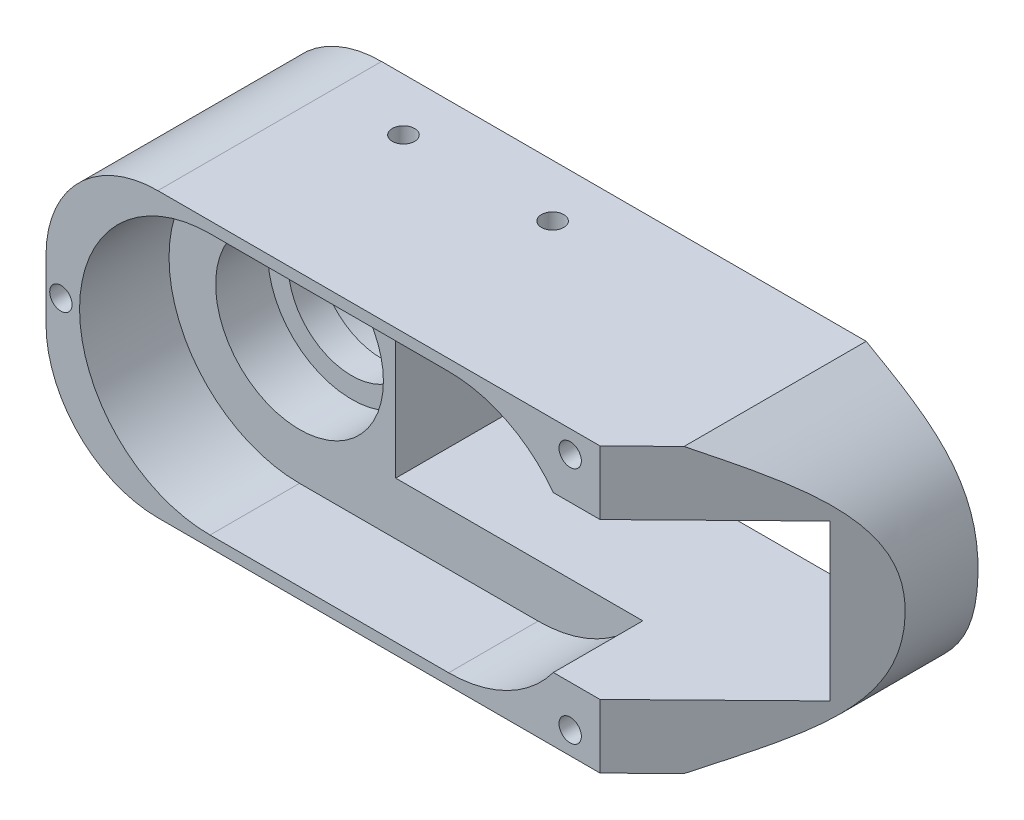
SolidWorks part; units mm, degrees
ref_plane "Front Plane" through (0, 0, 0) normal (0, 0, 1) x (1, 0, 0)
ref_plane "Top Plane" through (0, 0, 0) normal (0, 1, 0) x (1, 0, 0)
ref_plane "Right Plane" through (0, 0, 0) normal (1, 0, 0) x (0, 0, -1)
sketch "Sketch1" plane through (0, 0, 0) normal (0, 0, 1) x (1, 0, 0)
  line L1 (-50, 19) -> (30, 19)
  line L2 (-50, 19) -> (-50, -19)
  line L3 (-50, -19) -> (30, -19)
  spline S0 degree 3 poles (30, 19) (36.5612, 15.2119) (45.1601, 10.8287) (44.9676, -11.0883) (37.933, -14.4199) (30, -19) knots 0 0 0 0 0.445629 0.545629 1 1 1 1
  point P5 (-50, 0)
  dimension "D1" = 80
  dimension "D2" = 38
  dimension "D3" = 50
extrude "Extrude1" add sketch "Sketch1" along normal blind 30
sketch "Sketch2" plane through (0, 0, 30) normal (0, 0, 1) x (1, 0, 0)
  line L0 (-28, 17.5) -> (4, 17.5)
  line L1 (4, -17.5) -> (-28, -17.5)
  line L2 (-50, 19) -> (-50, -19) construction
  arc A0 (-28, 17.5) -> (-28, -17.5) centre (-28, 0) ccw
  arc A1 (4, -17.5) -> (4, 17.5) centre (4, 0) ccw
  dimension "D1" = 35
  dimension "D4" = 17.5
  dimension "D2" = 22
  dimension "D3" = 32
extrude "Extrude2" cut sketch "Sketch2" against normal blind 12
sketch "Sketch4" plane through (0, 0, 18) normal (0, 0, 1) x (1, 0, 0)
  line L0 (-28, 17.5) -> (-28, -17.5) construction
  circle A0 centre (-28, 0) radius 11.25
  arc A1 (-28, 17.5) -> (-28, -17.5) centre (-28, 0) ccw construction
  point P8 (0, 0)
  point P9 (-28, 0)
  dimension "D1" = 22.5
extrude "Extrude3" cut sketch "Sketch4" against normal blind 7
sketch "Sketch5" plane through (0, 0, 11) normal (0, 0, 1) x (1, 0, 0)
  circle A0 centre (-28, 0) radius 8.5
  circle A1 centre (-28, 0) radius 11.25 construction
  dimension "D1" = 17
extrude "Extrude4" cut sketch "Sketch5" against normal through all
sketch "Sketch6" plane through (0, 0, 0) normal (0, 0, -1) x (-1, 0, 0)
  circle A0 centre (28, 0) radius 11.25
  dimension "D1" = 22.5
extrude "Extrude5" cut sketch "Sketch6" against normal blind 7
sketch "Sketch8" plane through (0, 0, 18) normal (0, 0, 1) x (1, 0, 0)
  circle A0 centre (2, 0) radius 2.5
  circle A1 centre (-28, 0) radius 11.25 construction
  dimension "D1" = 5
  dimension "D2" = 30
extrude "Extrude6" cut sketch "Sketch8" against normal through all
sketch "Sketch7" plane through (0, 0, 0) normal (0, 0, -1) x (-1, 0, 0)
  line L0 (14.8, 0) -> (-2, 0) construction
  line L1 (-40.2, -10.4457) -> (14.8, -10.4457) construction
  line L2 (-40.2, -10.4457) -> (-40.2, 10.4457) construction
  line L3 (-40.2, 10.4457) -> (14.8, 10.4457) construction
  line L4 (14.8, -10.4457) -> (14.8, 10.4457) construction
  line L6 (7.8, 10.4457) -> (-33.2, 10.4457)
  line L7 (7.8, 10.4457) -> (7.8, -10.4457)
  line L8 (7.8, -10.4457) -> (-33.2, -10.4457)
  line L9 (-33.2, 10.4457) -> (-33.2, -10.4457)
  circle A1 centre (-2, 0) radius 2.5 construction
  point P14 (-12.7, -10.4457)
  point P15 (-12.7, -10.4457)
  dimension "D3" = 41
  dimension "D1" = 55
  dimension "D2" = 9.8
extrude "Extrude7" cut sketch "Sketch7" against normal through all
sketch "Sketch10" plane through (0, 0, 30) normal (0, 0, 1) x (1, 0, 0)
  line L0 (33.2, -10.4457) -> (18.0405, -10.4457) construction
  line L1 (39.9, -10.4457) -> (-15.1, -10.4457)
  line L2 (39.9, -10.4457) -> (39.9, 10.4457)
  line L3 (39.9, 10.4457) -> (-15.1, 10.4457)
  line L4 (-15.1, -10.4457) -> (-15.1, 10.4457)
  line L5 (18.0405, 10.4457) -> (33.2, 10.4457) construction
  line L9 (33.2, 10.4457) -> (33.2, -10.4457) construction
  dimension "D1" = 55
  dimension "D2" = 6.7
extrude "Extrude8" cut sketch "Sketch10" against normal blind 28
fillet "Fillet1" radius 15 2 edges at (-50, -19, 15) (-50, 19, 15)
sketch "Sketch17" plane through (0, 0, 0) normal (0, 1, 0) x (1, 0, 0)
  line L0 (55, 0) -> (55, -30)
  line L2 (55, -30) -> (24.2974, -30)
  line L3 (24.2974, -30) -> (55, 0)
extrude "Extrude17" cut sketch "Sketch17" against normal through all and the other way through all
sketch "Sketch19" plane through (0, 19, 0) normal (0, 1, 0) x (-1, 0, 0)
  line L1 (35, 0) -> (35, 30) construction
  circle A0 centre (5, 7.0599) radius 1.5
  circle A1 centre (25, 7.0599) radius 1.5
  dimension "D1" = 3
  dimension "D2" = 20
  dimension "D3" = 10
extrude "Extrude19" cut sketch "Sketch19" against normal blind 6
mirror "Mirror4" about plane through (0, 0, 0) normal (0, 1, 0) of "Extrude19"
hole_wizard "Ø4.5 (4.5) Diameter Hole1" positions "3DSketch1" profile "Sketch20" hole size "Ø4.5" standard "Ansi Metric"
sketch3d "3DSketch1"
  line L0 (33.2, -10.4457, 2) -> (39.9, -10.4457, 2) construction
  point P0 (36.0132, 5.0043, 2)
  point P2 (36.0132, -4.9957, 2)
  point P4 (-11.2468, 5.0043, 2)
  point P6 (-11.2468, -4.9957, 2)
  dimension "D1" = 10
  dimension "D2" = 47.26
  dimension "D3" = 5.45
sketch "Sketch20" plane through (36.0132, 5.0043, 2) normal (1, 0, 0) x (0, -1, 0)
  line L0 (0, 0) -> (0, 20)
  line L1 (0, 20) -> (2.25, 20)
  line L2 (2.25, 20) -> (2.25, 0)
  line L5 (2.25, 0) -> (0, 0)
  line L10 (0, 20) -> (-2.25, 20) construction
  line L11 (0, -6.35) -> (0, 107.95) construction
  dimension "Hole Dia." = 4.5
  dimension "Hole Depth" = 20
  dimension "Drill Angle" = 180
hole_wizard "Ø3.0 (3) Diameter Hole1" positions "3DSketch2" profile "Sketch21" hole size "Ø3.0" standard "Ansi Metric"
sketch3d "3DSketch2"
  line L0 (-50, 4, 30) -> (-50, -4, 30) construction
  line L1 (24.2974, 19, 30) -> (-35, 19, 30) construction
  line L2 (-35, -19, 30) -> (24.2974, -19, 30) construction
  line L3 (24.2974, -19, 30) -> (24.2974, -10.4457, 30) construction
  point P0 (-48, 0, 30)
  point P2 (20.2974, -16, 30)
  point P4 (20.2974, 16, 30)
  point P10 (-50, 0, 30)
  dimension "D1" = 2
  dimension "D2" = 3
  dimension "D3" = 3
  dimension "D4" = 4
sketch "Sketch21" plane through (-48, 0, 30) normal (1, 0, 0) x (0, -1, 0)
  line L0 (0, 0) -> (0, 20)
  line L1 (0, 20) -> (1.5, 20)
  line L2 (1.5, 20) -> (1.5, 0)
  line L5 (1.5, 0) -> (0, 0)
  line L10 (0, 20) -> (-1.5, 20) construction
  line L11 (0, -6.35) -> (0, 107.95) construction
  dimension "Hole Dia." = 3
  dimension "Hole Depth" = 20
  dimension "Drill Angle" = 180
